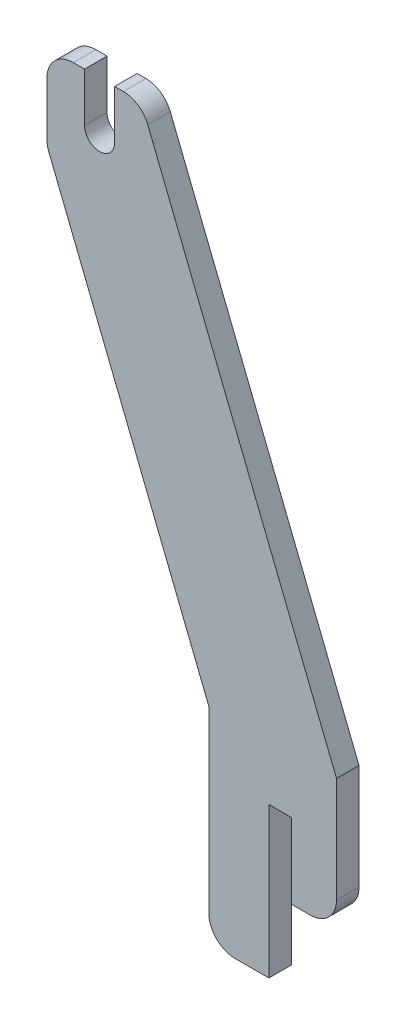
SolidWorks part; units mm, degrees
ref_plane "Plano frontal" through (0, 0, 0) normal (0, 0, 1) x (1, 0, 0)
ref_plane "Plano superior" through (0, 0, 0) normal (0, 1, 0) x (1, 0, 0)
ref_plane "Plano direito" through (0, 0, 0) normal (1, 0, 0) x (0, 0, -1)
sketch "Model" plane through (0, 0, 0) normal (0, 0, 1) x (1, 0, 0)
  line L0 (216.5876, 108.0909) -> (216.5876, 136.0909)
  line L1 (182.5876, 88.0909) -> (182.5876, 135.7922)
  line L2 (159.8484, 266.0909) -> (157.5187, 266.0909)
  line L3 (139.5187, 259.0909) -> (139.5187, 244.8125)
  line L4 (149.5187, 266.0909) -> (149.5187, 253.0909)
  line L5 (157.5187, 253.0909) -> (157.5187, 266.0909)
  line L6 (140.0194, 242.2127) -> (182.5876, 135.7922)
  line L7 (149.5187, 266.0909) -> (146.5187, 266.0909)
  line L8 (189.5876, 81.0909) -> (198.5876, 81.0909)
  line L9 (198.5876, 81.0909) -> (198.5876, 121.0909)
  line L10 (198.5876, 121.0909) -> (204.5876, 121.0909)
  line L11 (204.5876, 121.0909) -> (204.5876, 101.0909)
  line L12 (204.5876, 101.0909) -> (209.5876, 101.0909)
  line L13 (216.5876, 136.0909) -> (166.3477, 261.6906)
  arc A0 (149.5187, 253.0909) -> (157.5187, 253.0909) centre (153.5187, 253.0909) ccw
  arc A1 (209.5876, 101.0909) -> (216.5876, 108.0909) centre (209.5876, 108.0909) ccw
  arc A2 (139.5187, 244.8125) -> (140.0194, 242.2127) centre (146.5187, 244.8125) ccw
  arc A3 (182.5876, 88.0909) -> (189.5876, 81.0909) centre (189.5876, 88.0909) ccw
  arc A4 (146.5187, 266.0909) -> (139.5187, 259.0909) centre (146.5187, 259.0909) ccw
  arc A5 (166.3477, 261.6906) -> (159.8484, 266.0909) centre (159.8484, 259.0909) ccw
extrude "Ressalto-extrusão1" add sketch "Model" along normal blind 6
